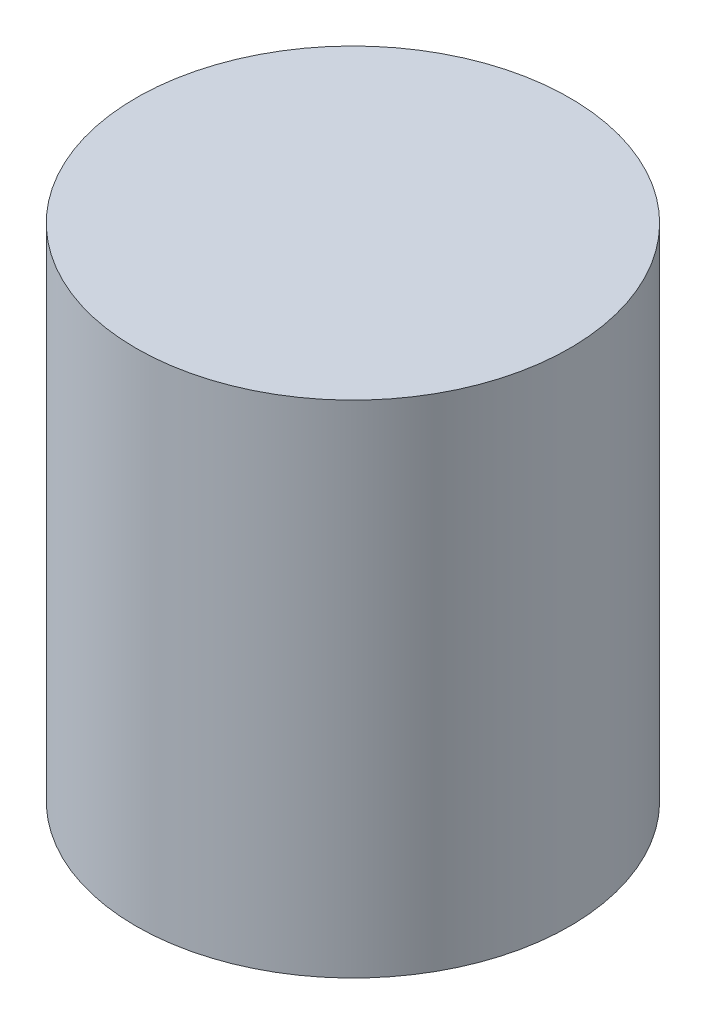
SolidWorks part; units mm, degrees
ref_plane "Front Plane" through (0, 0, 0) normal (0, 0, 1) x (1, 0, 0)
ref_plane "Top Plane" through (0, 0, 0) normal (0, 1, 0) x (1, 0, 0)
ref_plane "Right Plane" through (0, 0, 0) normal (1, 0, 0) x (0, 0, -1)
sketch "Sketch1" plane through (0, 0, 0) normal (0, 1, 0) x (1, 0, 0)
  circle A0 centre (0, 0) radius 130
  dimension "D1" = 260
extrude "Boss-Extrude1" add sketch "Sketch1" against normal blind 300
sketch "Sketch2" plane through (0, -300, 0) normal (0, -1, 0) x (-1, 0, 0)
  circle A0 centre (0, 0) radius 125
  dimension "D1" = 250
extrude "Cut-Extrude1" cut sketch "Sketch2" against normal blind 280
